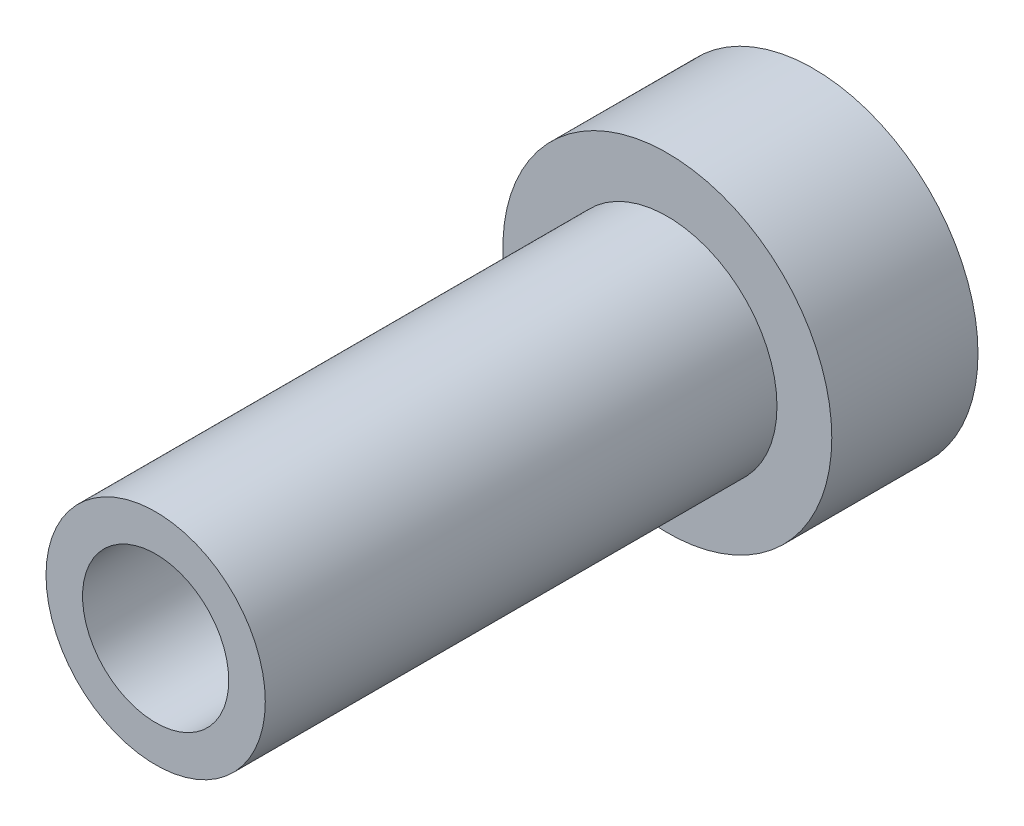
SolidWorks part; units mm, degrees
ref_plane "Ön Düzlem" through (0, 0, 0) normal (0, 0, 1) x (1, 0, 0)
ref_plane "Üst Düzlem" through (0, 0, 0) normal (0, 1, 0) x (1, 0, 0)
ref_plane "Sağ Düzlem" through (0, 0, 0) normal (1, 0, 0) x (0, 0, -1)
sketch "Çizim1" plane through (0, 0, 0) normal (0, 0, 1) x (1, 0, 0)
  circle A0 centre (0, 0) radius 2.25
  dimension "D1" = 4.5
extrude "Yükseklik-Ekstrüzyon1" add sketch "Çizim1" along normal blind 2
sketch "Çizim2" plane through (0, 0, 2) normal (0, 0, 1) x (1, 0, 0)
  circle A0 centre (0, 0) radius 1.5
  circle A1 centre (0, 0) radius 1
  dimension "D1" = 3
  dimension "D2" = 2
extrude "Yükseklik-Ekstrüzyon2" add sketch "Çizim2" along normal blind 7
